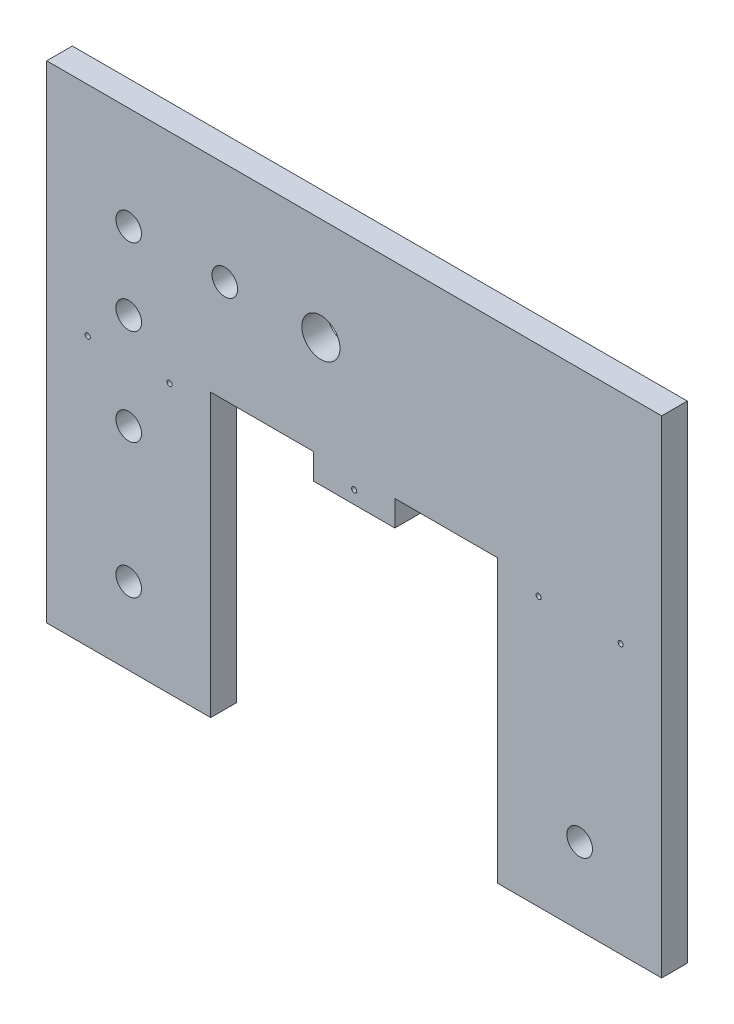
SolidWorks part; units mm, degrees
ref_plane "Front Plane" through (0, 0, 0) normal (0, 0, 1) x (1, 0, 0)
ref_plane "Top Plane" through (0, 0, 0) normal (0, 1, 0) x (1, 0, 0)
ref_plane "Right Plane" through (0, 0, 0) normal (1, 0, 0) x (0, 0, -1)
sketch "Sketch1" plane through (0, 0, 0) normal (0, 0, 1) x (1, 0, 0)
  line L0 (0, 69.85) -> (40.64, 69.85) construction
  line L1 (0, 0) -> (40.64, 0)
  line L2 (0, 69.85) -> (0, 120.65)
  line L3 (0, 120.65) -> (40.64, 120.65)
  line L4 (152.4, 69.85) -> (152.4, 120.65)
  line L5 (40.64, 120.65) -> (40.64, 69.85) construction
  line L6 (111.76, 120.65) -> (111.76, 69.85) construction
  line L7 (111.76, 120.65) -> (152.4, 120.65)
  line L8 (40.64, 120.65) -> (111.76, 120.65)
  line L9 (0, 69.85) -> (0, 0)
  line L10 (152.4, 69.85) -> (152.4, 0)
  line L11 (0, 95.25) -> (40.64, 95.25) construction
  line L12 (111.76, 95.25) -> (152.4, 95.25) construction
  line L13 (111.76, 0) -> (152.4, 0)
  line L14 (111.76, 69.85) -> (152.4, 69.85) construction
  line L15 (40.64, 0) -> (40.64, 63.5)
  line L16 (40.64, 69.85) -> (111.76, 69.85) construction
  line L17 (111.76, 63.5) -> (111.76, 0)
  line L18 (20.32, 120.65) -> (20.32, 0) construction
  line L19 (132.08, 120.65) -> (132.08, 0) construction
  line L20 (40.64, 95.25) -> (111.76, 95.25) construction
  line L21 (40.64, 63.5) -> (111.76, 63.5)
  line L22 (20.32, 19.05) -> (132.08, 19.05) construction
  circle A0 centre (20.32, 95.25) radius 3.175
  circle A1 centre (67.945, 95.25) radius 4.7371
  circle A2 centre (132.08, 19.05) radius 3.175
  circle A3 centre (20.32, 76.2) radius 3.175
  circle A4 centre (20.32, 52.3875) radius 3.175
  circle A6 centre (20.32, 19.05) radius 3.175
  circle A7 centre (44.1325, 95.25) radius 3.175
  dimension "D5" = 23.8125
  dimension "D6" = 23.8125
  dimension "D7" = 6.35
  dimension "D9" = 23.8125
  dimension "D10" = 9.4742
  dimension "D1" = 152.4
  dimension "D2" = 50.8
  dimension "D3" = 40.64
  dimension "D4" = 120.65
  dimension "D8" = 19.05
  dimension "D11" = 33.3375
  dimension "D12" = 57.15
extrude "Boss-Extrude1" add sketch "Sketch1" along normal blind 6.35
sketch "Sketch2" plane through (0, 0, 6.35) normal (0, 0, 1) x (1, 0, 0)
  line L0 (0, 69.85) -> (40.64, 69.85) construction
  line L1 (40.64, 63.5) -> (66.1383, 63.5)
  line L2 (40.64, 63.5) -> (40.64, 69.85)
  line L3 (40.64, 69.85) -> (66.1383, 69.85)
  line L4 (66.1383, 63.5) -> (66.1383, 69.85)
  line L6 (111.76, 63.5) -> (86.2617, 63.5)
  line L7 (111.76, 63.5) -> (111.76, 69.85)
  line L8 (111.76, 69.85) -> (86.2617, 69.85)
  line L9 (86.2617, 63.5) -> (86.2617, 69.85)
extrude "Cut-Extrude1" cut sketch "Sketch2" against normal blind 6.35
sketch "Sketch4" plane through (0, 0, 6.35) normal (0, 0, 1) x (1, 0, 0)
  line L0 (76.2, 66.675) -> (76.2, 63.5) construction
  line L1 (66.1383, 66.675) -> (76.2, 66.675) construction
  line L4 (86.2617, 63.5) -> (86.2617, 69.85)
  line L5 (86.2617, 69.85) -> (66.1383, 69.85)
  line L6 (66.1383, 69.85) -> (66.1383, 63.5)
  line L7 (66.1383, 63.5) -> (86.2617, 63.5)
  line L8 (86.2617, 63.5) -> (86.2617, 69.85) construction
  line L9 (86.2617, 69.85) -> (66.1383, 69.85) construction
  line L10 (66.1383, 69.85) -> (66.1383, 63.5) construction
  line L11 (66.1383, 63.5) -> (86.2617, 63.5) construction
  circle A0 centre (76.2, 66.675) radius 0.635
  dimension "D1" = 0
extrude "Cut-Extrude3" cut sketch "Sketch4" against normal blind 6.35
sketch "Sketch6" plane through (0, 0, 6.35) normal (0, 0, 1) x (1, 0, 0)
  line L0 (20.32, 69.85) -> (0, 69.85) construction
  line L1 (0, 69.85) -> (0, 63.5) construction
  line L2 (20.32, 69.85) -> (-78.5412, 69.85) construction
  line L3 (10.16, 69.85) -> (10.16, 66.675) construction
  line L4 (111.76, 69.85) -> (111.76, 63.5)
  line L5 (111.76, 63.5) -> (152.4, 63.5)
  line L6 (152.4, 63.5) -> (152.4, 69.85)
  line L7 (152.4, 69.85) -> (111.76, 69.85)
  line L8 (111.76, 69.85) -> (111.76, 63.5) construction
  line L9 (111.76, 63.5) -> (152.4, 63.5) construction
  line L10 (152.4, 63.5) -> (152.4, 69.85) construction
  line L11 (121.92, 69.85) -> (121.92, 66.675) construction
  line L12 (40.64, 63.5) -> (40.64, 69.85)
  line L13 (40.64, 69.85) -> (0, 69.85)
  line L14 (0, 69.85) -> (0, 63.5)
  line L15 (0, 63.5) -> (40.64, 63.5)
  line L16 (40.64, 63.5) -> (40.64, 69.85) construction
  line L17 (40.64, 69.85) -> (0, 69.85) construction
  line L18 (0, 69.85) -> (0, 63.5) construction
  line L19 (0, 63.5) -> (40.64, 63.5) construction
  line L20 (10.16, 66.675) -> (30.4358, 66.675) construction
  line L21 (30.4358, 66.675) -> (40.64, 66.675) construction
  line L22 (30.4358, 67.31) -> (30.4358, 66.675) construction
  line L23 (152.4, 69.85) -> (132.08, 69.85) construction
  line L24 (132.08, 69.85) -> (111.76, 69.85) construction
  line L25 (121.92, 66.675) -> (142.24, 69.85) construction
  line L26 (142.24, 69.85) -> (142.24, 66.675) construction
  line L27 (121.92, 66.675) -> (111.76, 66.675) construction
  line L28 (142.24, 66.675) -> (152.4, 66.675) construction
  circle A0 centre (10.16, 66.675) radius 0.635
  circle A1 centre (30.4358, 66.675) radius 0.635
  circle A2 centre (121.92, 66.675) radius 0.635
  circle A3 centre (142.24, 66.675) radius 0.635
  dimension "D1" = 0
  dimension "D2" = 0
extrude "Cut-Extrude4" cut sketch "Sketch6" against normal blind 6.35
